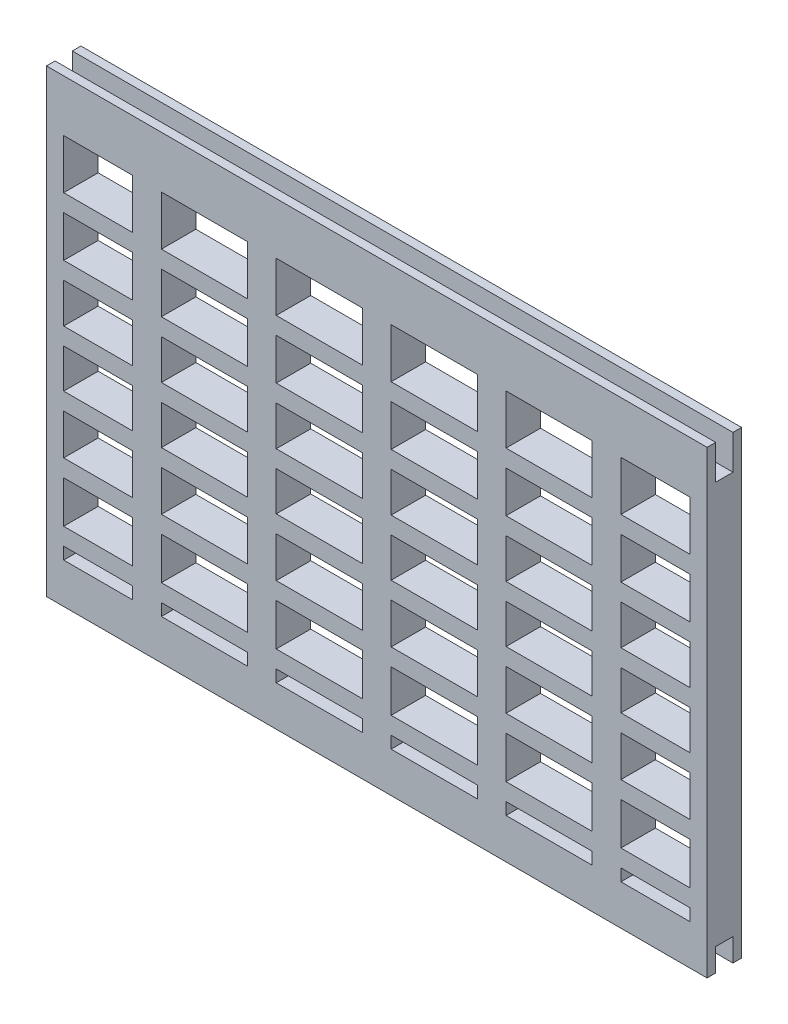
SolidWorks part; units mm, degrees
ref_plane "Plano frontal" through (0, 0, 0) normal (0, 0, 1) x (1, 0, 0)
ref_plane "Plano superior" through (0, 0, 0) normal (0, 1, 0) x (1, 0, 0)
ref_plane "Plano direito" through (0, 0, 0) normal (1, 0, 0) x (0, 0, -1)
sketch "Esboço1" plane through (0, 0, 0) normal (0, 0, 1) x (1, 0, 0)
  line L0 (-22.5, 30.2161) -> (-22.5, 21.5993)
  line L1 (-57.5, -36.7839) -> (57.5, -36.7839)
  line L2 (-57.5, -36.7839) -> (-57.5, 33.2161)
  line L3 (-57.5, 33.2161) -> (57.5, 33.2161)
  line L4 (57.5, -36.7839) -> (57.5, 33.2161)
  line L5 (-54.5, -33.7839) -> (-42.4915, -33.7839)
  line L6 (-54.5, -33.7839) -> (-54.5, -31.6856)
  line L7 (-54.5, 30.2161) -> (-42.4915, 30.2161)
  line L8 (54.5, -33.7839) -> (54.5, -31.6856)
  line L9 (-54.5, -1.5) -> (-42.4915, -1.5)
  line L10 (-37.4915, 21.5993) -> (-22.5, 21.5993)
  line L11 (-54.5, 1.5) -> (-42.4915, 1.5)
  line L12 (54.5, -8.3137) -> (54.5, -1.5)
  line L13 (-54.5, 21.5993) -> (-42.4915, 21.5993)
  line L14 (-37.4915, 18.5993) -> (-22.5, 18.5993)
  line L15 (-54.5, 18.5993) -> (-42.4915, 18.5993)
  line L16 (54.5, 21.5993) -> (54.5, 18.5993)
  line L17 (-54.5, -28.6856) -> (-42.4915, -28.6856)
  line L18 (-37.4915, 11.4017) -> (-22.5, 11.4017)
  line L19 (-54.5, 11.4017) -> (-42.4915, 11.4017)
  line L20 (-37.4915, 8.4017) -> (-22.5, 8.4017)
  line L21 (-54.5, 8.4017) -> (-42.4915, 8.4017)
  line L22 (42.5, 8.4017) -> (42.5, 1.5)
  line L23 (-54.5, -31.6856) -> (-42.4915, -31.6856)
  line L24 (54.5, 11.4017) -> (54.5, 30.2161)
  line L25 (-54.5, -8.3137) -> (-42.4915, -8.3137)
  line L26 (-37.4915, -8.3137) -> (-22.5, -8.3137)
  line L27 (-54.5, -11.3137) -> (-42.4915, -11.3137)
  line L28 (54.5, -18.3754) -> (54.5, -11.3137)
  line L29 (-37.4915, 30.2161) -> (-22.5, 30.2161)
  line L30 (-2.5, 30.2161) -> (-2.5, 21.5993)
  line L31 (-54.5, -18.3754) -> (-42.4915, -18.3754)
  line L32 (-37.4915, -11.3137) -> (-22.5, -11.3137)
  line L33 (-54.5, -21.3754) -> (-42.4915, -21.3754)
  line L34 (54.5, -28.6856) -> (54.5, -21.3754)
  line L35 (22.502, -18.3754) -> (37.5, -18.3754)
  line L36 (2.5, 30.2161) -> (2.5, 21.5993)
  line L37 (-42.4915, 30.2161) -> (-42.4915, 21.5993)
  line L38 (-42.4915, -31.6856) -> (-42.4915, -33.7839)
  line L39 (-40.1106, -1.5) -> (-39.8886, -1.5)
  line L40 (-37.4915, 30.2161) -> (-37.4915, 21.5993)
  line L41 (-37.4915, -31.6856) -> (-37.4915, -33.7839)
  line L42 (-42.4915, -21.3754) -> (-42.4915, -28.6856)
  line L43 (17.498, 30.2161) -> (17.498, 21.5993)
  line L44 (22.502, 30.2161) -> (37.7564, 30.2161)
  line L45 (2.5, -33.7839) -> (17.498, -33.7839)
  line L46 (42.5, 30.2161) -> (42.5, 21.5993)
  line L47 (22.502, 30.2161) -> (22.502, 21.5993)
  line L48 (-22.5, -33.7839) -> (-22.3447, -31.6856) construction
  line L49 (-37.4915, -18.3754) -> (-22.5, -18.3754)
  line L50 (2.5, 11.4017) -> (17.498, 11.4017)
  line L51 (54.5, 1.5) -> (54.5, 8.4017)
  line L52 (37.5, 30.2161) -> (37.5, 21.5993)
  line L53 (-37.4915, -21.3754) -> (-22.5, -21.3754)
  line L54 (17.498, -33.7839) -> (17.6534, -31.6856) construction
  line L55 (-37.4915, -1.5) -> (-22.5, -1.5)
  line L56 (-37.4915, 1.5) -> (-22.5, 1.5)
  line L57 (22.3464, -31.6856) -> (37.6553, -31.6856)
  line L58 (-37.4915, -28.6856) -> (-22.5, -28.6856)
  line L59 (-37.4915, -31.6856) -> (-22.3447, -31.6856)
  line L60 (37.5, -33.7839) -> (37.6553, -31.6856) construction
  line L61 (-37.4915, -33.7839) -> (-22.5, -33.7839)
  line L62 (-17.5, 30.2161) -> (-17.5, 21.5993)
  line L63 (-37.4915, -21.3754) -> (-37.4915, -28.6856)
  line L64 (-42.4915, -11.3137) -> (-42.4915, -18.3754)
  line L65 (-37.4915, -11.3137) -> (-37.4915, -18.3754)
  line L66 (-42.4915, -1.5) -> (-42.4915, -8.3137)
  line L67 (-37.4915, -1.5) -> (-37.4915, -8.3137)
  line L68 (-42.4915, 8.4017) -> (-42.4915, 1.5)
  line L69 (-37.4915, 8.4017) -> (-37.4915, 1.5)
  line L70 (-42.4915, 18.5993) -> (-42.4915, 11.4017)
  line L71 (-37.4915, 18.5993) -> (-37.4915, 11.4017)
  line L72 (-22.5, 18.5993) -> (-22.5, 11.4017)
  line L73 (-17.5, -8.3137) -> (-2.5, -8.3137)
  line L74 (-17.5, 30.2161) -> (-2.5, 30.2161)
  line L75 (-17.5, 18.5993) -> (-17.5, 11.4017)
  line L76 (-17.5, 21.5993) -> (-2.5, 21.5993)
  line L77 (-17.5, 18.5993) -> (-2.5, 18.5993)
  line L78 (-17.5, 11.4017) -> (-2.5, 11.4017)
  line L79 (-17.5, 8.4017) -> (-2.5, 8.4017)
  line L80 (-17.5, -11.3137) -> (-2.5, -11.3137)
  line L81 (-20.111, -1.5) -> (-19.8928, -1.5)
  line L82 (-17.5, -18.3754) -> (-2.5, -18.3754)
  line L83 (-17.6555, -31.6856) -> (-17.5, -33.7839) construction
  line L84 (-17.5, -1.5) -> (-2.5, -1.5)
  line L85 (-17.5, 1.5) -> (-2.5, 1.5)
  line L86 (-17.5, -21.3754) -> (-2.5, -21.3754)
  line L87 (2.5, 21.5993) -> (17.498, 21.5993)
  line L88 (2.5, 18.5993) -> (2.5, 11.4017)
  line L89 (2.5, 18.5993) -> (17.498, 18.5993)
  line L90 (-2.5, 18.5993) -> (-2.5, 11.4017)
  line L91 (17.498, 18.5993) -> (17.498, 11.4017)
  line L92 (42.5, 8.4017) -> (54.5, 8.4017)
  line L93 (22.502, 11.4017) -> (37.5, 11.4017)
  line L94 (22.502, 18.5993) -> (22.502, 11.4017)
  line L95 (22.502, 21.5993) -> (37.5, 21.5993)
  line L96 (22.502, 18.5993) -> (37.5, 18.5993)
  line L97 (22.502, 8.4017) -> (37.5, 8.4017)
  line L98 (-22.5, -21.3754) -> (-22.5, -28.6856)
  line L99 (-17.5, -21.3754) -> (-17.5, -28.6856)
  line L100 (-22.5, -11.3137) -> (-22.5, -18.3754)
  line L101 (-17.5, -11.3137) -> (-17.5, -18.3754)
  line L102 (-22.5, -1.5) -> (-22.5, -8.3137)
  line L103 (-17.5, -1.5) -> (-17.5, -8.3137)
  line L104 (-2.5, -1.5) -> (-2.5, -8.3137)
  line L105 (2.5, -1.5) -> (2.5, -8.3137)
  line L106 (17.498, -1.5) -> (17.498, -8.3137)
  line L107 (19.998, -0.0271) -> (20.1073, -1.5) construction
  line L108 (42.5, 11.4017) -> (54.5, 11.4017)
  line L109 (22.502, -1.5) -> (22.502, -8.3137)
  line L110 (37.5, -1.5) -> (37.5, -18.3754)
  line L111 (37.5, 8.4017) -> (37.5, 1.5)
  line L112 (22.502, 8.4017) -> (22.502, 1.5)
  line L113 (42.5, -1.5) -> (42.5, -18.3754)
  line L114 (-2.5, -21.3754) -> (-2.5, -28.6856)
  line L115 (2.5, -21.3754) -> (2.5, -28.6856)
  line L116 (17.498, -21.3754) -> (17.498, -28.6856)
  line L117 (21.5816, -21.3754) -> (37.5, -21.3754)
  line L118 (42.5, -18.3754) -> (54.5, -18.3754)
  line L119 (22.502, -21.3754) -> (22.502, -28.6856)
  line L120 (37.5, -21.3754) -> (37.5, -28.6856)
  line L121 (17.498, 8.4017) -> (17.498, 1.5)
  line L122 (42.5, -33.7839) -> (54.5, -33.7839)
  line L123 (42.5, -21.3754) -> (42.5, -28.6856)
  line L124 (-22.5, -31.6856) -> (-22.5, -33.7839)
  line L125 (-17.5, -31.6856) -> (-17.5, -33.7839)
  line L126 (-2.5, -31.6856) -> (-2.5, -33.7839)
  line L127 (2.5, -31.6856) -> (2.5, -33.7839)
  line L128 (17.498, -31.6856) -> (17.498, -33.7839)
  line L129 (42.5, -21.3754) -> (54.5, -21.3754)
  line L130 (22.3464, -31.6856) -> (22.502, -33.7839) construction
  line L131 (22.502, -31.6856) -> (22.502, -33.7839)
  line L132 (37.5, -31.6856) -> (37.5, -33.7839)
  line L133 (42.5, -28.6856) -> (54.5, -28.6856)
  line L134 (42.3445, -31.6856) -> (42.5, -33.7839) construction
  line L135 (42.5, -31.6856) -> (42.5, -33.7839)
  line L136 (-17.5, -28.6856) -> (-2.5, -28.6856)
  line L137 (-17.6555, -31.6856) -> (-2.5, -31.6856)
  line L138 (-17.5, -33.7839) -> (-2.5, -33.7839)
  line L139 (2.5, -28.6856) -> (17.498, -28.6856)
  line L140 (2.5, -31.6856) -> (17.6534, -31.6856)
  line L141 (2.5, -18.3754) -> (17.498, -18.3754)
  line L142 (2.5, -21.3754) -> (17.498, -21.3754)
  line L143 (2.5, -8.3137) -> (17.498, -8.3137)
  line L144 (2.5, -11.3137) -> (17.498, -11.3137)
  line L145 (-2.5, -11.3137) -> (-2.5, -18.3754)
  line L146 (2.5, -11.3137) -> (2.5, -18.3754)
  line L147 (17.498, -11.3137) -> (17.498, -18.3754)
  line L148 (19.8889, -1.5) -> (19.998, -0.0271) construction
  line L149 (42.3445, -31.6856) -> (54.5, -31.6856)
  line L150 (22.502, -11.3137) -> (22.502, -18.3754)
  line L151 (22.502, -8.3137) -> (37.5, -8.3137)
  line L152 (22.502, -11.3137) -> (37.5, -11.3137)
  line L153 (22.502, -33.7839) -> (37.5, -33.7839)
  line L154 (22.502, -28.6856) -> (37.5, -28.6856)
  line L155 (42.5, -11.3137) -> (54.5, -11.3137)
  line L156 (42.5, -8.3137) -> (54.5, -8.3137)
  line L157 (42.5, -1.5) -> (54.5, -1.5)
  line L158 (42.5, 1.5) -> (54.5, 1.5)
  line L159 (2.5, 8.4017) -> (17.498, 8.4017)
  line L160 (42.5, 18.5993) -> (54.5, 18.5993)
  line L161 (42.5, 21.5993) -> (54.5, 21.5993)
  line L162 (42.236, 30.2161) -> (54.5, 30.2161)
  line L163 (-2.5, 8.4017) -> (-2.5, 1.5)
  line L164 (2.5, 8.4017) -> (2.5, 1.5)
  line L165 (-17.5, 8.4017) -> (-17.5, 1.5)
  line L166 (-22.5, 8.4017) -> (-22.5, 1.5)
  line L167 (22.502, 1.5) -> (37.5, 1.5)
  line L168 (22.502, -1.5) -> (37.5, -1.5)
  line L169 (19.8889, -1.5) -> (20.1073, -1.5)
  line L170 (37.5, 18.5993) -> (37.5, 11.4017)
  line L171 (42.5, 18.5993) -> (42.5, 11.4017)
  line L172 (2.5, 1.5) -> (17.498, 1.5)
  line L173 (2.5, -1.5) -> (17.498, -1.5)
  line L174 (-54.5, -28.6856) -> (-54.5, -21.3754)
  line L175 (-54.5, -18.3754) -> (-54.5, -11.3137)
  line L176 (-54.5, -8.3137) -> (-54.5, -1.5)
  line L177 (-54.5, 1.5) -> (-54.5, 8.4017)
  line L178 (-54.5, 11.4017) -> (-54.5, 18.5993)
  line L179 (-54.5, 21.5993) -> (-54.5, 30.2161)
  line L180 (2.5, 30.2161) -> (17.498, 30.2161)
  line L182 (-57.5, -36.7839) -> (57.5, -36.7839)
  line L183 (-57.5, -36.7839) -> (-57.5, -40.7839)
  line L184 (-57.5, -40.7839) -> (57.5, -40.7839)
  line L185 (57.5, -36.7839) -> (57.5, -40.7839)
  line L186 (-57.5, 33.2161) -> (57.5, 33.2161)
  line L187 (-57.5, 33.2161) -> (-57.5, 39.2161)
  line L188 (-57.5, 39.2161) -> (57.5, 39.2161)
  line L189 (57.5, 33.2161) -> (57.5, 39.2161)
  point P0 (0, 0)
  point P6 (0, 0)
  point P11 (0, 0)
  point P16 (0, 10)
  point P17 (0, 20)
  point P18 (0, -10)
  point P19 (0, -19.9887)
  point P20 (0, 20)
  point P25 (0, 10)
  point P30 (0, -10)
  point P35 (0, -19.9887)
  point P40 (0, -29.9887)
  point P41 (0, -29.9887)
  point P46 (0, 0)
  point P51 (-40, 0)
  point P52 (-20, 0)
  point P53 (20, 0)
  point P55 (40, 0)
  point P56 (-40, 0)
  point P62 (-20, 0)
  point P67 (20, 0)
  point P72 (40, 0)
  dimension "D1" = 115
  dimension "D2" = 70
  dimension "D3" = 3
  dimension "D4" = 3
  dimension "D5" = 3
  dimension "D6" = 3
  dimension "D7" = 4
  dimension "D8" = 6
  dimension "D13" = 5
  dimension "D14" = 20
  dimension "D15" = 20
  dimension "D16" = 20
  dimension "D17" = 20
  dimension "D18" = 5
  dimension "D19" = 5
  dimension "D20" = 5.0041
  dimension "D21" = 5
extrude "Ressalto-extrusão1" add sketch "Esboço1" along normal blind 6
sketch "Esboço2" plane through (0, 0, 0) normal (1, 0, 0) x (0, 0, -1)
  line L0 (-6, -40.7839) -> (0, -40.7839) construction
  line L1 (-4.5, -40.7839) -> (-1.5, -40.7839)
  line L2 (-4.5, -40.7839) -> (-4.5, -36.79)
  line L3 (-1.5, -40.7839) -> (-1.5, -36.79)
  line L4 (-4.5, -36.79) -> (-1.5, -36.79)
  line L5 (-6, 39.2161) -> (0, 39.2161) construction
  line L6 (-4.5, 39.2161) -> (-1.5, 39.2161)
  line L7 (-4.5, 39.2161) -> (-4.5, 33.2132)
  line L8 (-1.5, 39.2161) -> (-1.5, 33.2132)
  line L9 (-4.5, 33.2132) -> (-1.5, 33.2132)
  point P0 (-4.5, -40.7839)
  point P1 (-1.5, -40.7839)
  point P4 (-3, -36.7839)
  point P5 (-3, -40.7839)
  point P8 (-4.5, 39.2161)
  point P11 (-1.5, 39.2161)
  point P16 (-3, 33.2161)
  point P17 (-3, 39.2161)
  dimension "D1" = 1.5
  dimension "D2" = 1.5
  dimension "D3" = 4
  dimension "D4" = 1.5
  dimension "D5" = 1.5
  dimension "D6" = 6
extrude "Corte-extrusão1" cut sketch "Esboço2" against normal through all both and the other way through all
